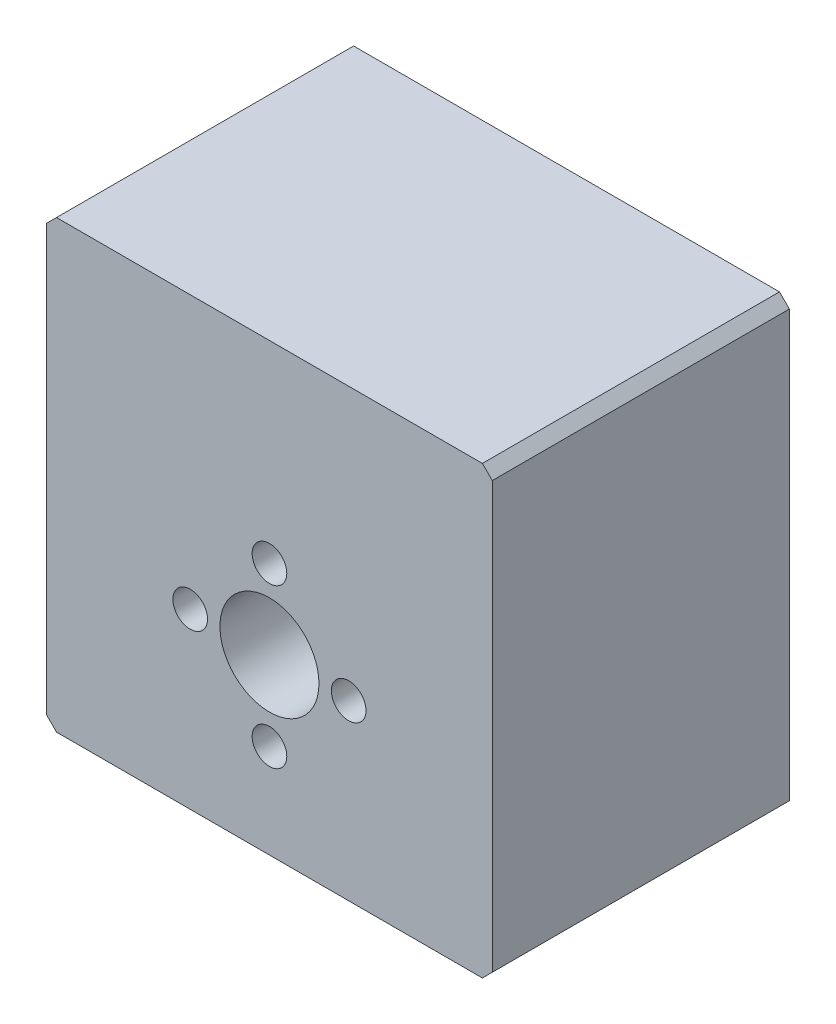
SolidWorks part; units mm, degrees
ref_plane "Front Plane" through (0, 0, 0) normal (0, 0, 1) x (1, 0, 0)
ref_plane "Top Plane" through (0, 0, 0) normal (0, 1, 0) x (1, 0, 0)
ref_plane "Right Plane" through (0, 0, 0) normal (1, 0, 0) x (0, 0, -1)
sketch "Sketch1" plane through (0, 0, 0) normal (0, 0, 1) x (1, 0, 0)
  line L0 (-22.5, 27.5) -> (22.5, 27.5)
  line L1 (22.5, 27.5) -> (22.5, -17.5)
  line L2 (22.5, -17.5) -> (-22.5, -17.5)
  line L3 (-22.5, -17.5) -> (-22.5, 27.5)
  circle A0 centre (0, 0) radius 5
extrude "Boss-Extrude1" add sketch "Sketch1" along normal mid plane 30
sketch "Sketch2" plane through (0, 0, 15) normal (0, 0, 1) x (1, 0, 0)
  circle A0 centre (0, 8) radius 1.75
  circle A1 centre (0, -8) radius 1.75
  circle A2 centre (8, 0) radius 1.75
  circle A3 centre (-8, 0) radius 1.75
extrude "Cut-Extrude1" cut sketch "Sketch2" against normal blind 10
chamfer "Chamfer1" distance 1 angle 45 4 edges at (-22.5, -17.5, 0) (-22.5, 27.5, 0) (22.5, -17.5, 0) (22.5, 27.5, 0)
sketch "Sketch3" plane through (0, -17.5, 0) normal (0, -1, 0) x (1, 0, 0)
  line L0 (24.75, 0) -> (-24.75, 0) construction
  line L1 (0, -16.5) -> (0, 16.5) construction
  circle A0 centre (15, 8) radius 2
  circle A1 centre (15, -8) radius 2
  dimension "D1" = 4
  dimension "D2" = 4
  dimension "D3" = 16
  dimension "D4" = 8
  dimension "D5" = 15
  dimension "D6" = 15
extrude "Cut-Extrude2" cut sketch "Sketch3" against normal blind 10
mirror "Mirror1" about plane through (0, 0, 0) normal (1, 0, 0) of "Cut-Extrude2"
